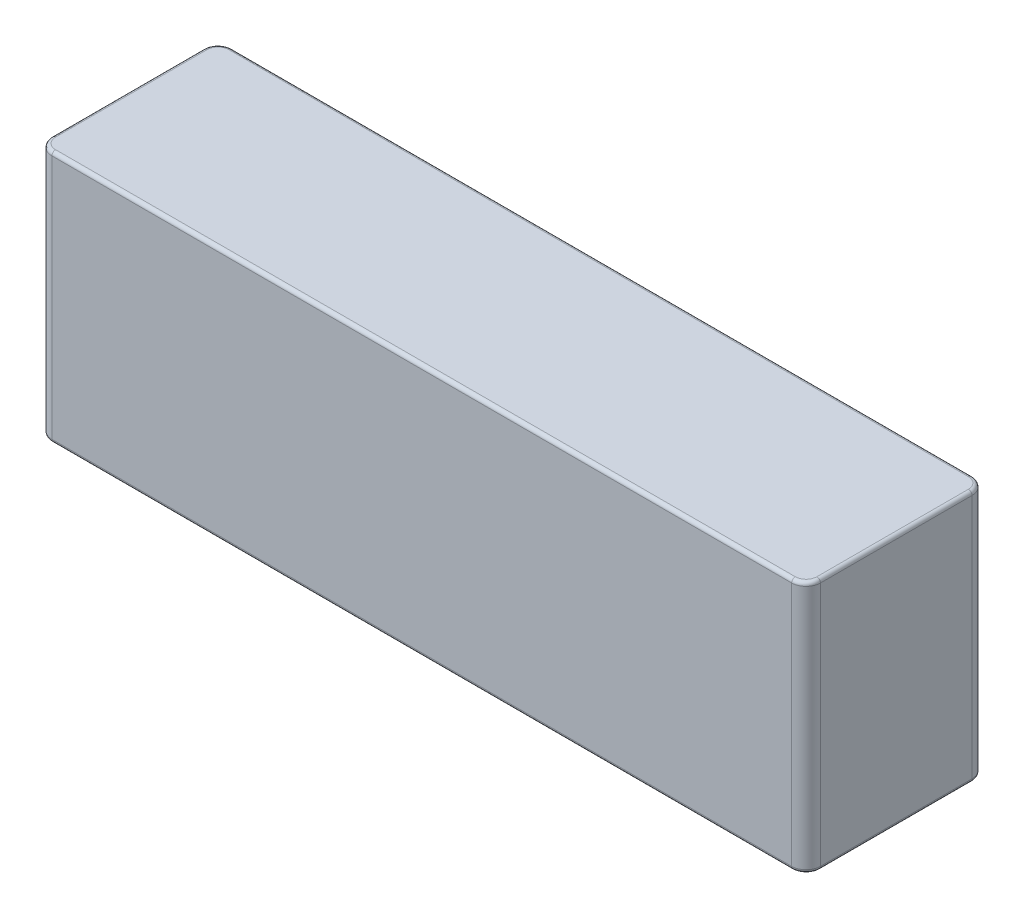
SolidWorks part; units mm, degrees
ref_plane "Front Plane" through (0, 0, 0) normal (0, 0, 1) x (1, 0, 0)
ref_plane "Top Plane" through (0, 0, 0) normal (0, 1, 0) x (1, 0, 0)
ref_plane "Right Plane" through (0, 0, 0) normal (1, 0, 0) x (0, 0, -1)
sketch "Sketch1" plane through (0, 0, 0) normal (0, 0, 1) x (1, 0, 0)
  line L1 (-53.25, 17.5) -> (53.25, 17.5)
  line L2 (-53.25, 17.5) -> (-53.25, -17.5)
  line L3 (-53.25, -17.5) -> (53.25, -17.5)
  line L4 (53.25, 17.5) -> (53.25, -17.5)
  line L5 (-53.25, 17.5) -> (53.25, -17.5) construction
  line L6 (-53.25, -17.5) -> (53.25, 17.5) construction
  point P0 (0, 0)
  dimension "D1" = 35
  dimension "D2" = 106.5
extrude "Boss-Extrude1" add sketch "Sketch1" along normal blind 25
fillet "Fillet1" radius 2 4 edges at (-53.25, 0, 0) (-53.25, 0, 25) (53.25, 0, 25) (53.25, 0, 0)
fillet "Fillet2" radius 0.5 16 edges at (-52.6642, -17.5, 24.4142) (-53.25, -17.5, 12.5) (-52.6642, -17.5, 0.5858) (0, -17.5, 0) (52.6642, -17.5, 0.5858) (53.25, -17.5, 12.5) (52.6642, -17.5, 24.4142) (52.6642, 17.5, 24.4142) (53.25, 17.5, 12.5) (52.6642, 17.5, 0.5858) (0, 17.5, 0) (-52.6642, 17.5, 0.5858) (-53.25, 17.5, 12.5) (-52.6642, 17.5, 24.4142) (0, -17.5, 25) (0, 17.5, 25)
